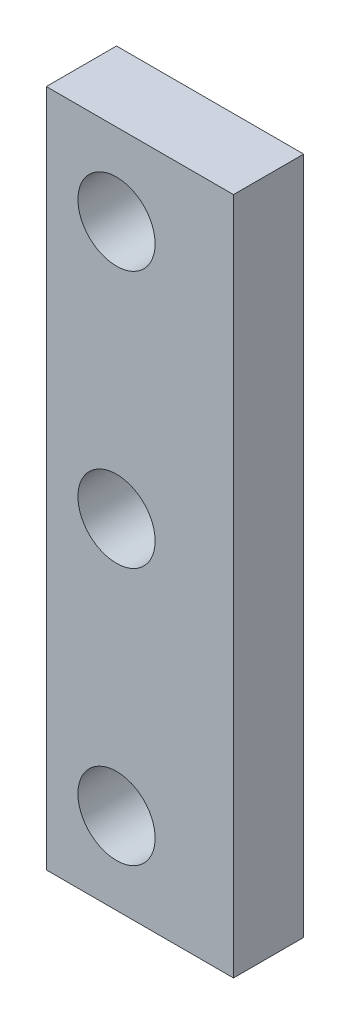
SolidWorks part; units mm, degrees
ref_plane "Plano frontal" through (0, 0, 0) normal (0, 0, 1) x (1, 0, 0)
ref_plane "Plano superior" through (0, 0, 0) normal (0, 1, 0) x (1, 0, 0)
ref_plane "Plano direito" through (0, 0, 0) normal (1, 0, 0) x (0, 0, -1)
sketch "Esboço1" plane through (0, 0, 0) normal (0, 0, 1) x (1, 0, 0)
  line L0 (0, 0) -> (8, 0) construction
  line L1 (0, 14.5) -> (8, 14.5)
  line L2 (0, 14.5) -> (0, -14.5)
  line L3 (0, -14.5) -> (8, -14.5)
  line L4 (8, 14.5) -> (8, -14.5)
  line L5 (0, 14.5) -> (8, -14.5) construction
  line L6 (0, -14.5) -> (8, 14.5) construction
  circle A0 centre (3, 11) radius 1.65
  circle A1 centre (3, 0) radius 1.65
  circle A2 centre (3, -11) radius 1.65
  dimension "D2" = 3.3
  dimension "D1" = 11
  dimension "D3" = 29
  dimension "D4" = 8
  dimension "D5" = 3
extrude "Ressalto-extrusão1" add sketch "Esboço1" along normal blind 3
